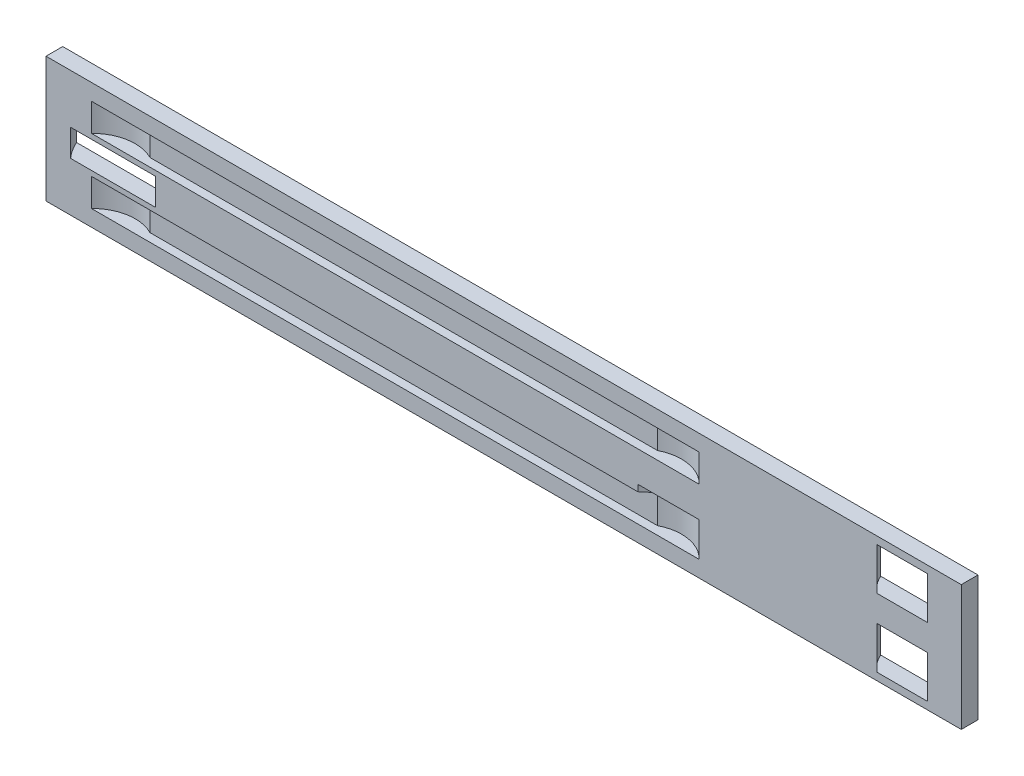
SolidWorks part; units mm, degrees
ref_plane "Alzado" through (0, 0, 0) normal (0, 0, 1) x (1, 0, 0)
ref_plane "Planta" through (0, 0, 0) normal (0, 1, 0) x (1, 0, 0)
ref_plane "Vista lateral" through (0, 0, 0) normal (1, 0, 0) x (0, 0, -1)
sketch "Croquis1" plane through (0, 0, 0) normal (0, 0, 1) x (1, 0, 0)
  line L0 (0, 0) -> (0, 135)
  line L1 (0, 135) -> (985, 135)
  line L2 (985, 135) -> (985, 0)
  line L3 (985, 0) -> (0, 0)
  dimension "D1" = 135
  dimension "D2" = 985
extrude "Saliente-Extruir1" add sketch "Croquis1" along normal blind 18
ref_plane "Plano1" through (0, 8, 0) normal (0, -1, 0) x (-1, 0, 0)
sketch "Croquis2" plane through (0, 8, 0) normal (0, -1, 0) x (-1, 0, 0)
  line L0 (-921.5, -18) -> (-921.5, 18) construction
  line L1 (-985, -18) -> (0, -18) construction
  line L2 (-985, -18) -> (-985, 0) construction
  circle A0 centre (-921.5, 18) radius 45
  dimension "D2" = 63.5
  dimension "D1" = 36
extrude "Cortar-Extruir1" cut sketch "Croquis2" against normal blind 45.5
ref_plane "Plano2" through (0, 67.5, 0) normal (0, 1, 0) x (1, 0, 0)
mirror "Simetría1" about plane through (0, 67.5, 0) normal (0, 1, 0) of "Cortar-Extruir1"
sketch "Croquis4" plane through (0, 67.5, 0) normal (0, 1, 0) x (1, 0, 0)
  line L0 (72.2, -18) -> (72.2, 24.2) construction
  line L1 (985, -18) -> (0, -18) construction
  line L2 (0, -18) -> (0, 0) construction
  circle A0 centre (72.2, 24.2) radius 62.2
  dimension "D2" = 72.2
  dimension "D1" = 42.2
extrude "Cortar-Extruir2" cut sketch "Croquis4" against normal mid plane 29
ref_plane "Plano3" through (0, 102.5, 0) normal (0, 1, 0) x (1, 0, 0)
sketch "Croquis5" plane through (0, 102.5, 0) normal (0, 1, 0) x (1, 0, 0)
  line L0 (82, 0) -> (82, -50) construction
  line L1 (0, 0) -> (985, 0) construction
  line L2 (0, -18) -> (0, 0) construction
  line L3 (102.8567, 0) -> (102.8567, -9) construction
  line L5 (102.8567, -9) -> (649.0525, -9)
  line L6 (48.9546, -18) -> (702.9546, -18)
  line L7 (0, -18) -> (985, -18) construction
  line L8 (375.9546, -18) -> (375.9546, 101.3461) construction
  arc A0 (102.8567, -9) -> (48.9546, -18) centre (82, -50) ccw
  arc A1 (649.0525, -9) -> (702.9546, -18) centre (669.9092, -50) cw
  dimension "D2" = 82
  dimension "D1" = 50
  dimension "D3" = 654
extrude "Cortar-Extruir3" cut sketch "Croquis5" against normal mid plane 30
mirror "Simetría5" about plane through (0, 67.5, 0) normal (0, 1, 0) of "Cortar-Extruir3"
sketch "Croquis7" plane through (0, 47.5, 0) normal (0, -1, 0) x (1, 0, 0)
  circle A0 centre (669.9092, 50) radius 46
  arc A1 (649.0525, 9) -> (702.9546, 18) centre (669.9092, 50) ccw construction
extrude "Cortar-Extruir4" cut sketch "Croquis7" against normal blind 7
